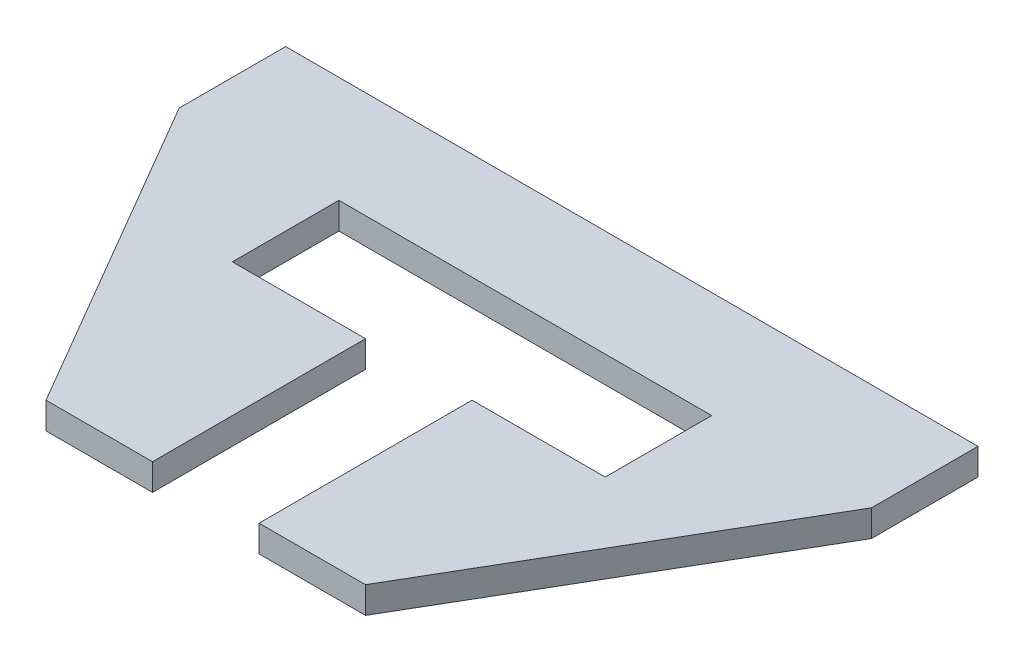
SolidWorks part; units mm, degrees
ref_plane "Front Plane" through (0, 0, 0) normal (0, 0, 1) x (1, 0, 0)
ref_plane "Top Plane" through (0, 0, 0) normal (0, 1, 0) x (1, 0, 0)
ref_plane "Right Plane" through (0, 0, 0) normal (1, 0, 0) x (0, 0, -1)
sketch "Sketch2" plane through (0, 0, 0) normal (0, 1, 0) x (1, 0, 0)
  line L1 (-153.2106, 73.0926) -> (11.8894, 73.0926)
  line L2 (-153.2106, 73.0926) -> (-153.2106, -28.5074)
  line L3 (-153.2106, -28.5074) -> (11.8894, -28.5074)
  line L4 (11.8894, 73.0926) -> (11.8894, -28.5074)
extrude "Boss-Extrude1" add sketch "Sketch2" along normal blind 6.35 contours L3 L4 L1 L2
sketch "Sketch3" plane through (0, 6.35, 0) normal (0, 1, 0) x (1, 0, 0)
  line L0 (-153.2106, -28.5074) -> (11.8894, -28.5074) construction
  line L1 (-83.3606, -28.5074) -> (-57.9606, -28.5074)
  line L2 (-83.3606, -28.5074) -> (-83.3606, 47.6926)
  line L3 (-83.3606, 47.6926) -> (-57.9606, 47.6926)
  line L4 (-57.9606, -28.5074) -> (-57.9606, 47.6926)
  dimension "D1" = 69.85
  dimension "D2" = 69.85
  dimension "D3" = 25.4
  dimension "D4" = 76.2
extrude "Cut-Extrude2" cut sketch "Sketch3" against normal through all
sketch "Sketch5" plane through (0, 6.35, 0) normal (0, 1, 0) x (1, 0, 0)
  line L1 (-115.1106, 47.6926) -> (-26.2106, 47.6926)
  line L2 (-115.1106, 47.6926) -> (-115.1106, 22.2926)
  line L3 (-115.1106, 22.2926) -> (-26.2106, 22.2926)
  line L4 (-26.2106, 47.6926) -> (-26.2106, 22.2926)
  line L9 (-153.2106, -28.5074) -> (-83.3606, -28.5074) construction
  line L10 (11.8894, 73.0926) -> (11.8894, -28.5074) construction
  dimension "D1" = 88.9
  dimension "D2" = 25.4
  dimension "D3" = 180
  dimension "D4" = 50.8
  dimension "D5" = 38.1
extrude "Cut-Extrude3" cut sketch "Sketch5" against normal through all
sketch "Sketch6" plane through (0, 6.35, 0) normal (0, 1, 0) x (1, 0, 0)
  line L0 (-153.2106, -28.5074) -> (-108.7606, -28.5074)
  line L1 (-153.2106, -28.5074) -> (-83.3606, -28.5074) construction
  line L2 (-108.7606, -28.5074) -> (-153.2106, 47.6926)
  line L3 (-153.2106, 73.0926) -> (-153.2106, -28.5074) construction
  line L4 (-153.2106, 47.6926) -> (-153.2106, -28.5074)
  dimension "D1" = 44.45
  dimension "D2" = 76.2
extrude "Cut-Extrude4" cut sketch "Sketch6" against normal through all
sketch "Sketch7" plane through (0, 6.35, 0) normal (0, 1, 0) x (1, 0, 0)
  line L0 (11.8894, -28.5074) -> (11.8894, 47.6926)
  line L1 (11.8894, 73.0926) -> (11.8894, -28.5074) construction
  line L2 (11.8894, 47.6926) -> (-32.5606, -28.5074)
  line L3 (-57.9606, -28.5074) -> (11.8894, -28.5074) construction
  line L4 (-32.5606, -28.5074) -> (11.8894, -28.5074)
  dimension "D1" = 44.45
  dimension "D2" = 76.2
extrude "Cut-Extrude5" cut sketch "Sketch7" against normal through all
